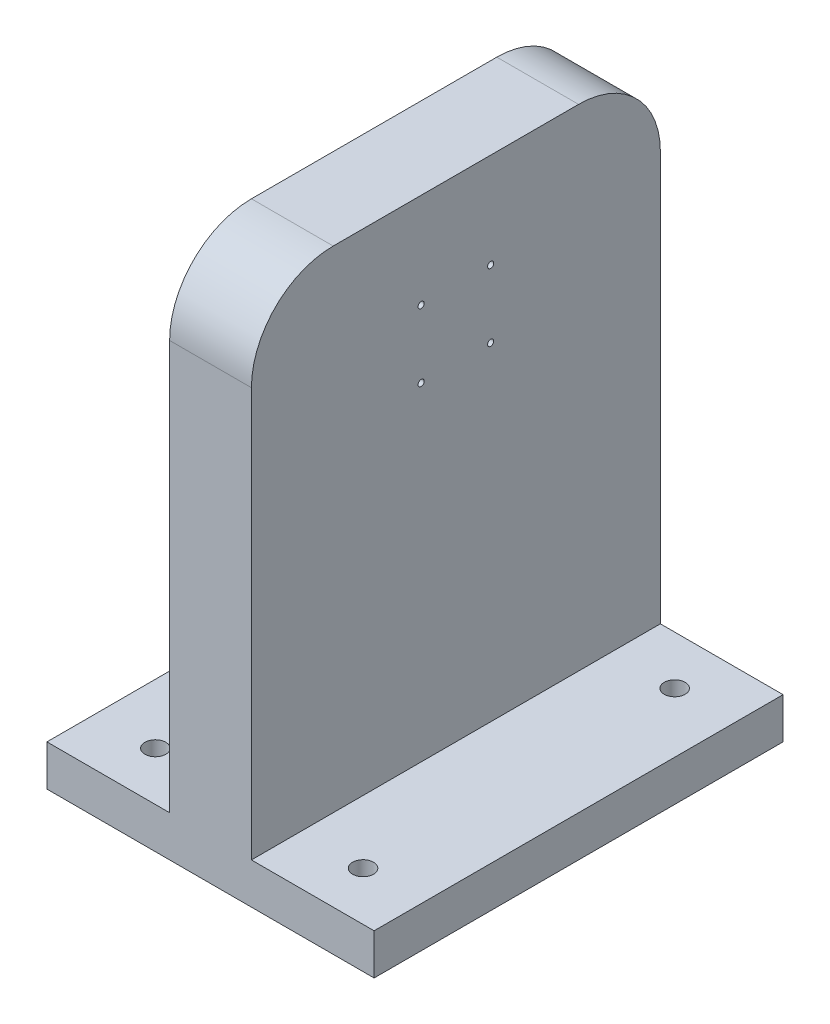
SolidWorks part; units mm, degrees
ref_plane "Front Plane" through (0, 0, 0) normal (0, 0, 1) x (1, 0, 0)
ref_plane "Top Plane" through (0, 0, 0) normal (0, 1, 0) x (1, 0, 0)
ref_plane "Right Plane" through (0, 0, 0) normal (1, 0, 0) x (0, 0, -1)
sketch "Sketch2" plane through (0, 0, 0) normal (0, 1, 0) x (1, 0, 0)
  line L1 (-40, -50) -> (40, -50)
  line L2 (-40, -50) -> (-40, 50)
  line L3 (-40, 50) -> (40, 50)
  line L4 (40, -50) -> (40, 50)
  line L5 (-40, -50) -> (40, 50) construction
  line L6 (-40, 50) -> (40, -50) construction
  point P0 (0, 0)
  dimension "D1" = 100
  dimension "D2" = 80
extrude "Boss-Extrude1" add sketch "Sketch2" along normal blind 10 contours L2 L3 L4 L1
sketch "Sketch3" plane through (0, 10, 0) normal (0, 1, 0) x (1, 0, 0)
  line L0 (-40, 50) -> (40, 50) construction
  line L1 (-10, -50) -> (10, -50)
  line L2 (-10, -50) -> (-10, 50)
  line L3 (-10, 50) -> (10, 50)
  line L4 (10, -50) -> (10, 50)
  line L5 (-10, -50) -> (10, 50) construction
  line L6 (-10, 50) -> (10, -50) construction
  point P0 (0, 0)
  dimension "D1" = 20
extrude "Boss-Extrude2" add sketch "Sketch3" along normal blind 120
sketch "Sketch4" plane through (-10, 0, 0) normal (-1, 0, 0) x (0, 0, 1)
  line L0 (0, 130) -> (0, 0) construction
  line L1 (-50, 130) -> (50, 130) construction
  line L2 (-50, 98.5) -> (50, 98.5) construction
  line L3 (-50, 130) -> (-50, 10) construction
  line L4 (50, 130) -> (50, 10) construction
  line L5 (50, 0) -> (-50, 0) construction
  line L11 (-8.5, 90.25) -> (8.5, 90.25) construction
  line L13 (-8.5, 90.25) -> (-8.5, 106.75) construction
  line L14 (-8.5, 106.75) -> (8.5, 106.75) construction
  line L15 (8.5, 90.25) -> (8.5, 106.75) construction
  line L16 (-8.5, 90.25) -> (8.5, 106.75) construction
  line L17 (-8.5, 106.75) -> (8.5, 90.25) construction
  circle A2 centre (-8.5, 106.75) radius 0.75
  circle A3 centre (-8.5, 90.25) radius 0.75
  circle A4 centre (8.5, 90.25) radius 0.75
  circle A5 centre (8.5, 106.75) radius 0.75
  point P13 (0, 98.5)
  point P14 (0, 98.5)
  dimension "D4" = 1.5
  dimension "D5" = 1.5
  dimension "D1" = 98.5
  dimension "D2" = 17
  dimension "D3" = 16.5
sketch "Sketch5" plane through (0, 0, 0) normal (0, -1, 0) x (1, 0, 0)
  line L0 (0, 50) -> (0, -50) construction
  line L1 (-40, 50) -> (40, 50) construction
  line L2 (-40, -50) -> (40, -50) construction
  line L3 (-40, 0) -> (40, 0) construction
  line L4 (-40, 50) -> (-40, -50) construction
  line L5 (40, 50) -> (40, -50) construction
  line L6 (-40, 38.1) -> (40, 38.1) construction
  line L7 (-40, -38.1) -> (40, -38.1) construction
  line L8 (-25.4, 50) -> (-25.4, -50) construction
  line L9 (25.4, 50) -> (25.4, -50) construction
  circle A0 centre (-25.4, -38.1) radius 2.555
  circle A1 centre (25.4, -38.1) radius 2.555
  circle A2 centre (-25.4, 38.1) radius 2.555
  circle A3 centre (25.4, 38.1) radius 2.555
  dimension "D5" = 5.11
  dimension "D1" = 76.2
  dimension "D2" = 38.1
  dimension "D3" = 50.8
  dimension "D4" = 25.4
extrude "Cut-Extrude2" cut sketch "Sketch5" against normal blind 55 contours A2 | A0 | A1 | A3
fillet "Fillet2" radius 20 2 edges at (0, 130, -50) (0, 130, 50)
extrude "Cut-Extrude3" cut sketch "Sketch4" against normal through all contours A2 | A4 | A5 | A3
